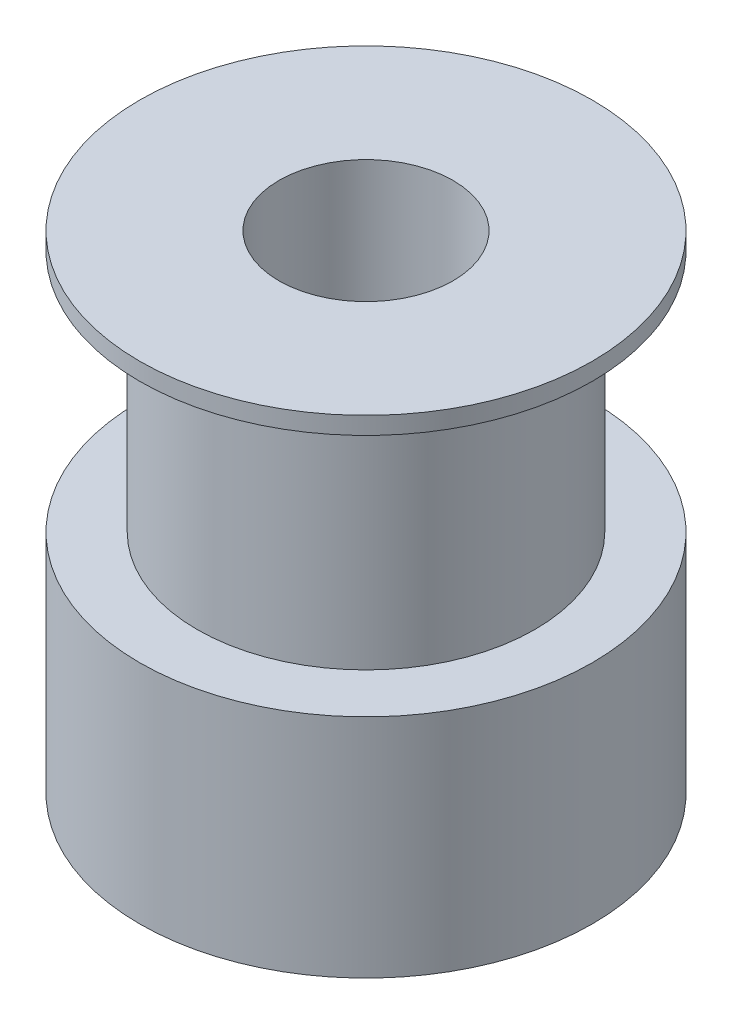
SolidWorks part; units mm, degrees
ref_plane "前视基准面" through (0, 0, 0) normal (0, 0, 1) x (1, 0, 0)
ref_plane "上视基准面" through (0, 0, 0) normal (0, 1, 0) x (1, 0, 0)
ref_plane "右视基准面" through (0, 0, 0) normal (1, 0, 0) x (0, 0, -1)
sketch "草图1" plane through (0, 0, 0) normal (0, 1, 0) x (1, 0, 0)
  circle A0 centre (0, 0) radius 6.5
  dimension "D1" = 13
extrude "凸台-拉伸1" add sketch "草图1" along normal blind 6.5
sketch "草图2" plane through (0, 6.5, 0) normal (0, 1, 0) x (1, 0, 0)
  circle A0 centre (0, 0) radius 4.85
extrude "凸台-拉伸2" add sketch "草图2" along normal blind 7
sketch "草图3" plane through (0, 13.5, 0) normal (0, 1, 0) x (1, 0, 0)
  circle A0 centre (0, 0) radius 6.5
extrude "凸台-拉伸3" add sketch "草图3" along normal blind 0.5
sketch "草图4" plane through (0, 14, 0) normal (0, 1, 0) x (1, 0, 0)
  circle A0 centre (0, 0) radius 2.5
extrude "切除-拉伸1" cut sketch "草图4" against normal through all
